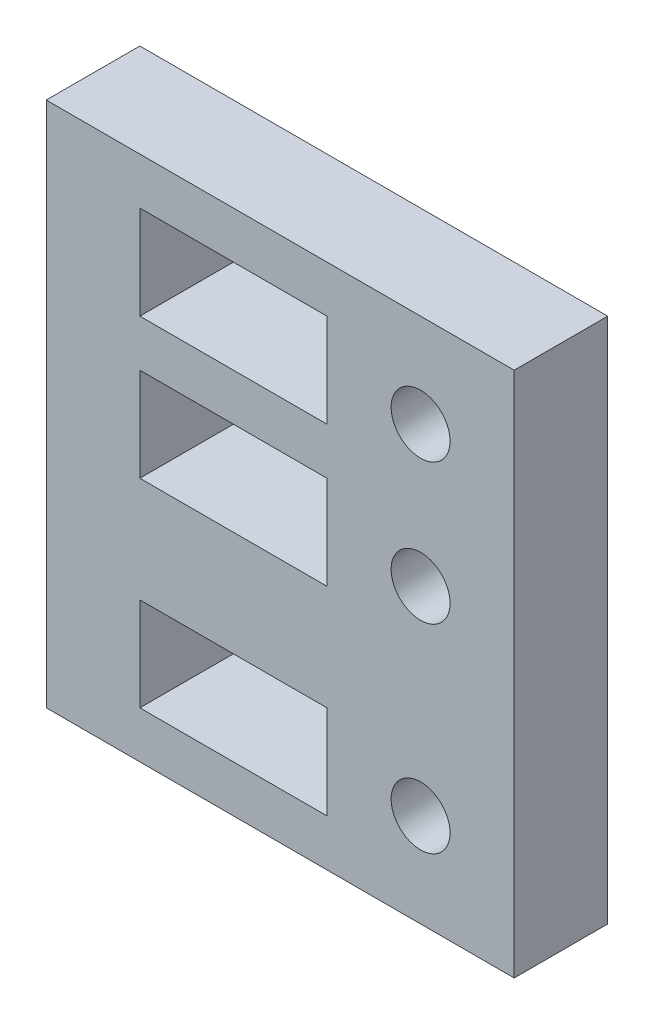
SolidWorks part; units mm, degrees
ref_plane "Front Plane" through (0, 0, 0) normal (0, 0, 1) x (1, 0, 0)
ref_plane "Top Plane" through (0, 0, 0) normal (0, 1, 0) x (1, 0, 0)
ref_plane "Right Plane" through (0, 0, 0) normal (1, 0, 0) x (0, 0, -1)
sketch "Sketch1" plane through (0, 0, 0) normal (0, 0, 1) x (1, 0, 0)
  line L0 (0, 35.7188) -> (0, 26.1938)
  line L1 (0, 0) -> (31.75, 0)
  line L2 (0, 0) -> (0, 26.1938)
  line L3 (6.35, 26.1938) -> (19.05, 26.1938) construction
  line L4 (31.75, 0) -> (31.75, 26.1937)
  line L5 (6.35, 23.0187) -> (19.05, 23.0187)
  line L6 (6.35, 23.0187) -> (6.35, 16.6687)
  line L7 (6.35, 16.6687) -> (19.05, 16.6687)
  line L8 (19.05, 23.0187) -> (19.05, 16.6687)
  line L9 (6.35, 9.525) -> (19.05, 9.525)
  line L10 (6.35, 9.525) -> (6.35, 3.175)
  line L11 (6.35, 3.175) -> (19.05, 3.175)
  line L12 (19.05, 9.525) -> (19.05, 3.175)
  line L13 (19.05, 26.1938) -> (6.35, 26.1938)
  line L14 (19.05, 26.1938) -> (19.05, 32.5437)
  line L15 (6.35, 32.5438) -> (0, 32.5438) construction
  line L16 (6.35, 26.1938) -> (6.35, 32.5438)
  line L17 (0, 35.7188) -> (31.75, 35.7188)
  line L18 (31.75, 35.7188) -> (31.75, 26.1937)
  line L19 (6.35, 32.5438) -> (19.05, 32.5437)
  line L20 (6.35, 32.5438) -> (6.35, 26.1938) construction
  circle A0 centre (25.4, 19.8437) radius 2
  circle A1 centre (25.4, 6.35) radius 2
  circle A2 centre (25.4, 29.3687) radius 2
  dimension "D12" = 6.35
  dimension "D13" = 4
  dimension "D14" = 4
  dimension "D15" = 4
  dimension "D1" = 6.35
  dimension "D2" = 6.35
  dimension "D3" = 26.1937
  dimension "D4" = 3.175
  dimension "D5" = 3.175
  dimension "D6" = 6.35
  dimension "D7" = 6.35
  dimension "D8" = 12.7
  dimension "D9" = 12.7
  dimension "D10" = 31.75
  dimension "D11" = 6.35
  dimension "D16" = 6.35
  dimension "D17" = 3.175
  dimension "D18" = 9.525
  dimension "D19" = 7.1437
extrude "Boss-Extrude1" add sketch "Sketch1" along normal blind 6.35
